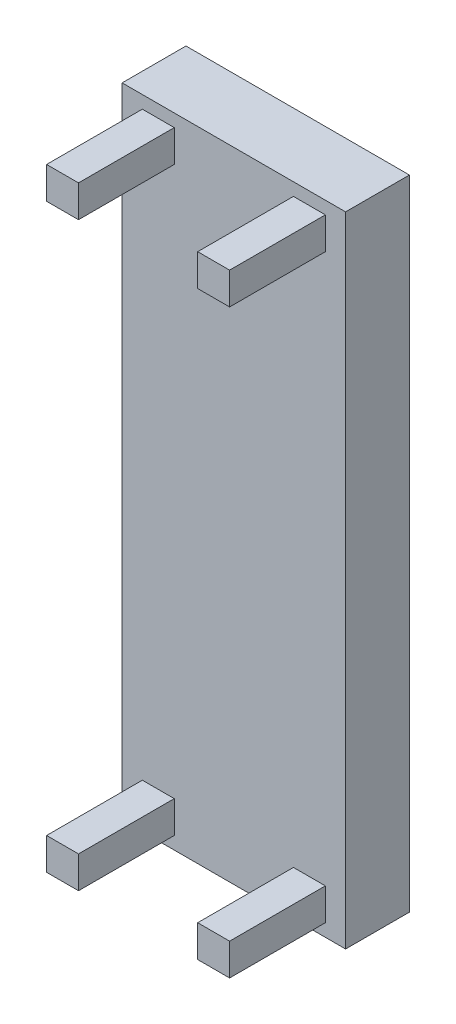
SolidWorks part; units mm, degrees
ref_plane "前视基准面" through (0, 0, 0) normal (0, 0, 1) x (1, 0, 0)
ref_plane "上视基准面" through (0, 0, 0) normal (0, 1, 0) x (1, 0, 0)
ref_plane "右视基准面" through (0, 0, 0) normal (1, 0, 0) x (0, 0, -1)
sketch "草图1" plane through (0, 0, 0) normal (0, 0, 1) x (1, 0, 0)
  line L1 (-350, -1000) -> (350, -1000)
  line L2 (-350, -1000) -> (-350, 1000)
  line L3 (-350, 1000) -> (350, 1000)
  line L4 (350, -1000) -> (350, 1000)
  line L5 (-350, -1000) -> (350, 1000) construction
  line L6 (-350, 1000) -> (350, -1000) construction
  point P0 (0, 0)
  dimension "D1" = 2000
  dimension "D2" = 700
extrude "凸台-拉伸1" add sketch "草图1" along normal blind 200
sketch "草图2" plane through (0, 0, 200) normal (0, 0, 1) x (1, 0, 0)
  line L1 (-286.6939, 960.2853) -> (-186.6939, 960.2853)
  line L2 (-286.6939, 960.2853) -> (-286.6939, 860.2853)
  line L3 (-286.6939, 860.2853) -> (-186.6939, 860.2853)
  line L4 (-186.6939, 960.2853) -> (-186.6939, 860.2853)
  line L5 (-286.6939, 960.2853) -> (-186.6939, 860.2853) construction
  line L6 (-286.6939, 860.2853) -> (-186.6939, 960.2853) construction
  line L8 (286.6939, 860.2853) -> (186.6939, 960.2853) construction
  line L9 (286.6939, 960.2853) -> (186.6939, 860.2853) construction
  line L10 (186.6939, 960.2853) -> (186.6939, 860.2853)
  line L11 (286.6939, 860.2853) -> (186.6939, 860.2853)
  line L12 (286.6939, 960.2853) -> (286.6939, 860.2853)
  line L13 (286.6939, 960.2853) -> (186.6939, 960.2853)
  line L14 (286.6939, -960.2853) -> (186.6939, -860.2853) construction
  line L15 (286.6939, -860.2853) -> (186.6939, -960.2853) construction
  line L16 (-286.6939, -860.2853) -> (-186.6939, -960.2853) construction
  line L17 (-286.6939, -960.2853) -> (-186.6939, -860.2853) construction
  line L18 (286.6939, -960.2853) -> (186.6939, -960.2853)
  line L19 (286.6939, -960.2853) -> (286.6939, -860.2853)
  line L20 (286.6939, -860.2853) -> (186.6939, -860.2853)
  line L21 (186.6939, -960.2853) -> (186.6939, -860.2853)
  line L22 (-186.6939, -960.2853) -> (-186.6939, -860.2853)
  line L23 (-286.6939, -860.2853) -> (-186.6939, -860.2853)
  line L24 (-286.6939, -960.2853) -> (-286.6939, -860.2853)
  line L25 (-286.6939, -960.2853) -> (-186.6939, -960.2853)
  point P0 (-236.6939, 910.2853)
  point P14 (236.6939, 910.2853)
  point P23 (236.6939, -910.2853)
  point P24 (-236.6939, -910.2853)
  dimension "D1" = 100
  dimension "D2" = 100
extrude "凸台-拉伸2" add sketch "草图2" along normal blind 300
